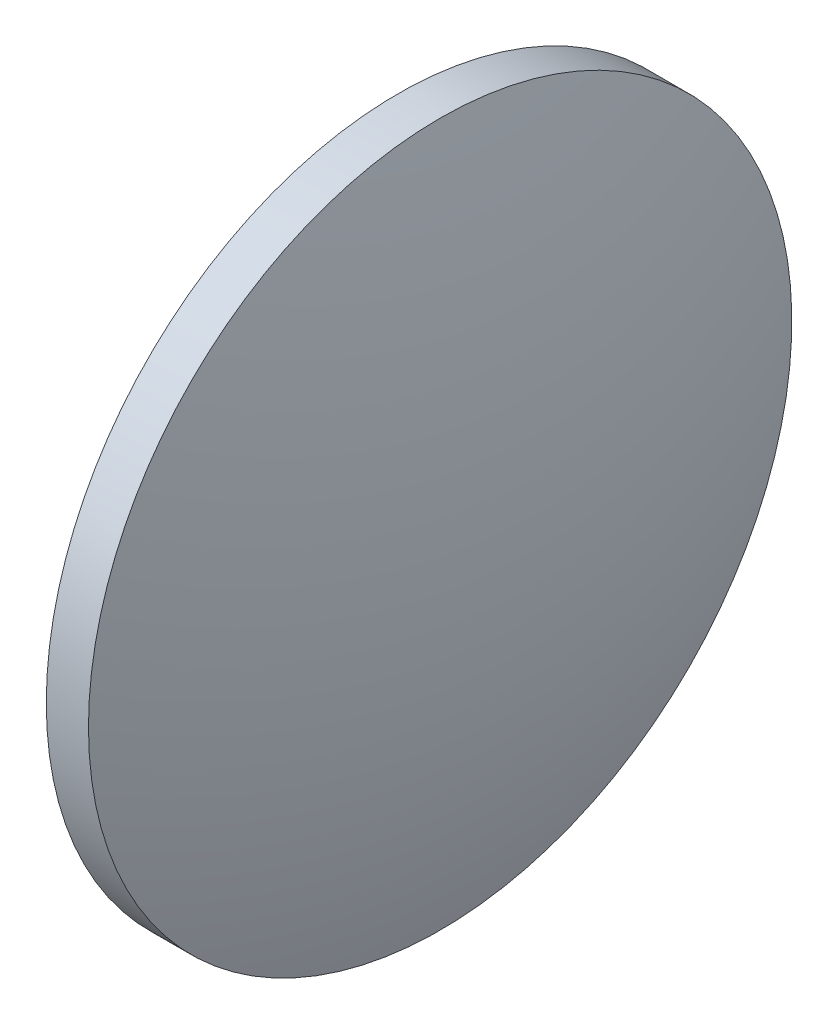
SolidWorks part; units mm, degrees
ref_plane "前视基准面" through (0, 0, 0) normal (0, 0, 1) x (1, 0, 0)
ref_plane "上视基准面" through (0, 0, 0) normal (0, 1, 0) x (1, 0, 0)
ref_plane "右视基准面" through (0, 0, 0) normal (1, 0, 0) x (0, 0, -1)
sketch "草图1" plane through (0, 0, 0) normal (0, 0, 1) x (1, 0, 0)
  line L0 (406.3891, 102.3012) -> (433.2806, 102.3012) construction
  line L1 (415.8114, 102.3012) -> (415.8114, 127.3012)
  line L2 (422.6814, 102.3012) -> (415.8114, 102.3012)
  line L5 (415.8114, 127.3012) -> (418.8114, 127.3012)
  arc A0 (422.6814, 102.3012) -> (418.8114, 127.3012) centre (339.997, 102.3012) ccw
revolve "旋转1" add sketch "草图1" angle 360 about L0
